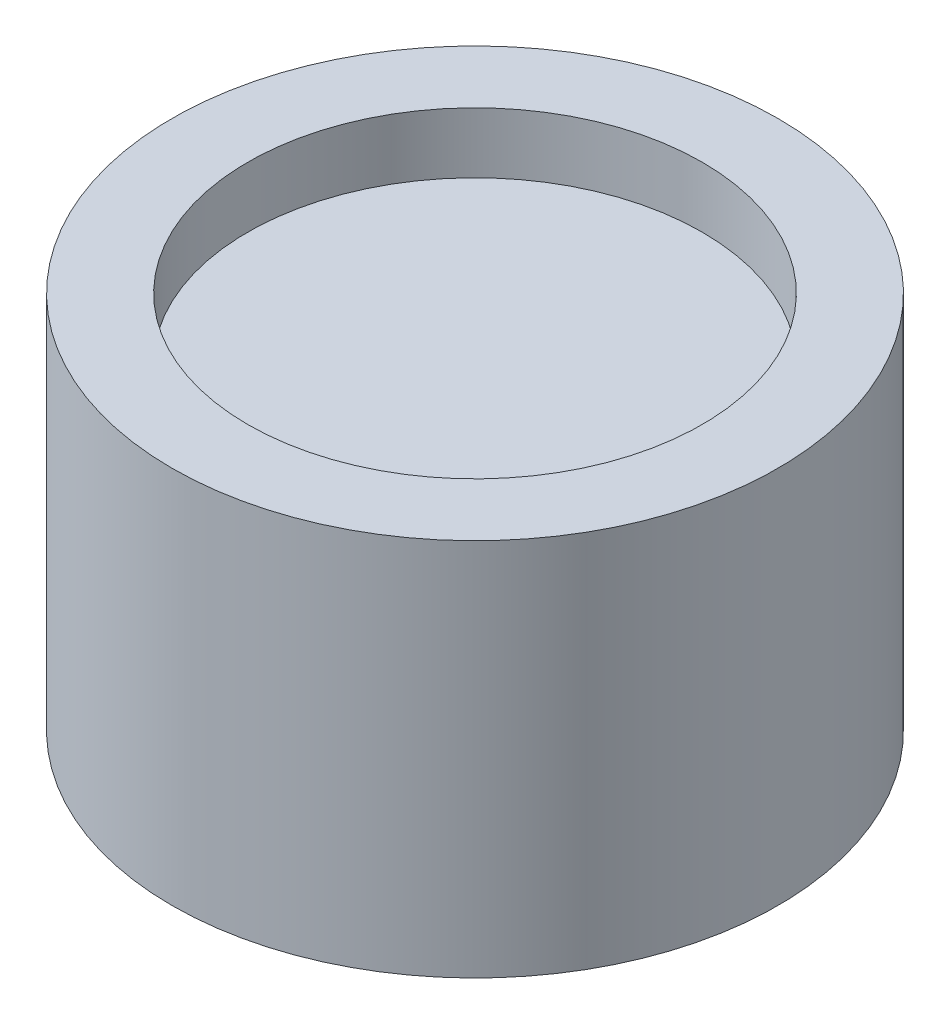
SolidWorks part; units mm, degrees
ref_plane "Plano frontal" through (0, 0, 0) normal (0, 0, 1) x (1, 0, 0)
ref_plane "Plano superior" through (0, 0, 0) normal (0, 1, 0) x (1, 0, 0)
ref_plane "Plano direito" through (0, 0, 0) normal (1, 0, 0) x (0, 0, -1)
sketch "Esboço1" plane through (0, 0, 0) normal (0, 0, 1) x (1, 0, 0)
  line L0 (0, 0) -> (0, 596.1298) construction
  line L1 (0, 0) -> (807.0529, 0) construction
  line L2 (150, 250) -> (200, 250)
  line L3 (200, 250) -> (200, 0)
  line L4 (200, 0) -> (0, 0)
  line L5 (0, 210) -> (0, 0)
  line L6 (150, 250) -> (150, 210)
  line L7 (150, 210) -> (0, 210)
  dimension "D1" = 400
  dimension "D2" = 250
  dimension "D3" = 40
  dimension "D4" = 300
revolve "Revolução1" add sketch "Esboço1" angle 360 about L0
sketch "Esboço2" plane through (0, 0, 0) normal (0, 0, 1) x (1, 0, 0)
  line L0 (0, 0) -> (0, 250) construction
  line L1 (150, 250) -> (-150, 250) construction
  line L2 (-50, 40) -> (50, 40)
  line L3 (50, 40) -> (50, 0)
  line L4 (-200, 0) -> (200, 0) construction
  line L5 (50, 0) -> (-50, 0)
  line L6 (-50, 40) -> (-50, 0)
  point P12 (0, 40)
  dimension "D1" = 100
  dimension "D2" = 40
extrude "Corte-extrusão1" [suppressed] cut sketch "Esboço2" against normal through all both and the other way through all
sketch "Esboço3" plane through (0, 0, 0) normal (0, -1, 0) x (1, 0, 0)
  line L1 (71, -55) -> (-71, -55) construction
  line L2 (71, -55) -> (71, 55) construction
  line L3 (71, 55) -> (-71, 55) construction
  line L4 (-71, -55) -> (-71, 55) construction
  line L5 (71, -55) -> (-71, 55) construction
  line L6 (71, 55) -> (-71, -55) construction
  circle A0 centre (-71, 55) radius 8
  circle A1 centre (71, 55) radius 8
  circle A2 centre (71, -55) radius 8
  circle A3 centre (-71, -55) radius 8
  point P0 (0, 0)
  dimension "D3" = 16
  dimension "D1" = 110
  dimension "D2" = 142
extrude "Corte-extrusão2" cut sketch "Esboço3" against normal blind 10
